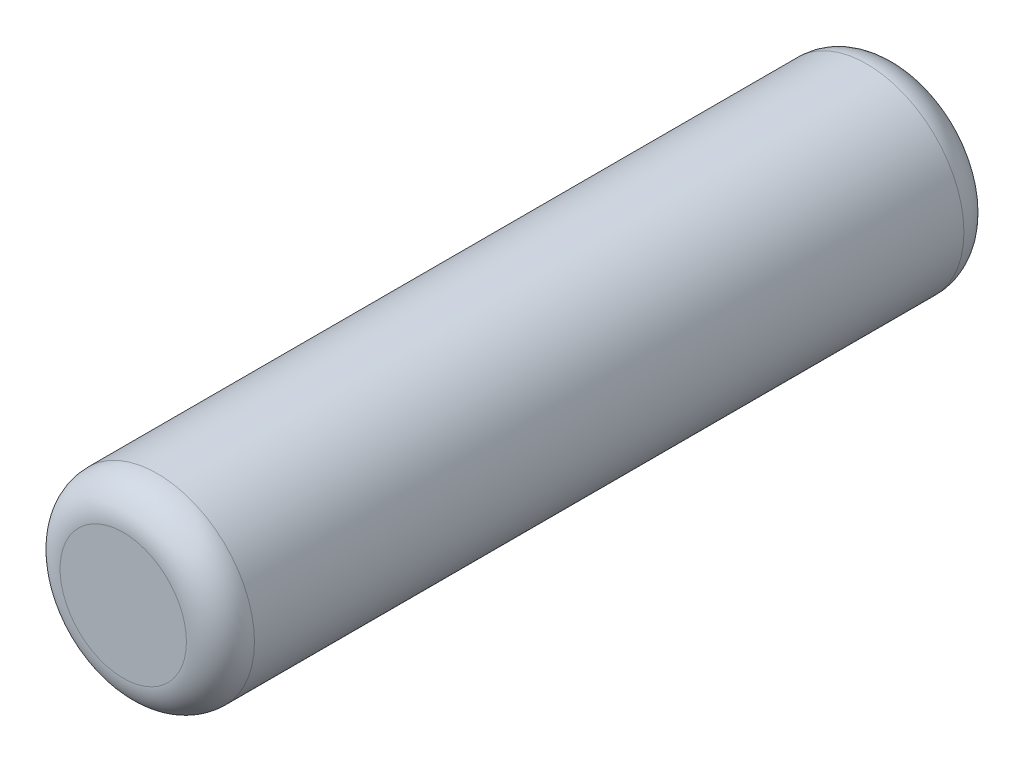
SolidWorks part; units mm, degrees
ref_plane "Front" through (0, 0, 0) normal (0, 0, 1) x (1, 0, 0)
ref_plane "Top" through (0, 0, 0) normal (0, 1, 0) x (1, 0, 0)
ref_plane "Right" through (0, 0, 0) normal (1, 0, 0) x (0, 0, -1)
sketch "Sketch1" plane through (0, 0, 0) normal (0, 0, 1) x (1, 0, 0)
  circle A0 centre (0, 0) radius 1
  dimension "D1" = 2
extrude "Boss-Extrude1" add sketch "Sketch1" along normal mid plane 8
fillet "Fillet1" radius 0.35 2 edges at (1, 0, -4) (1, 0, 4)
